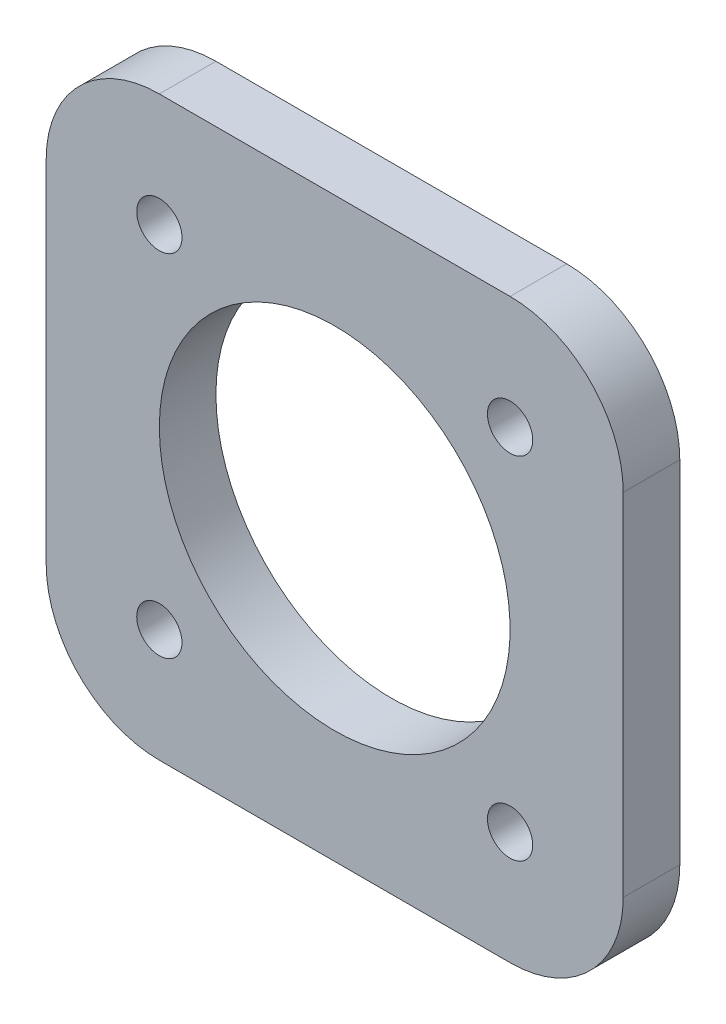
SolidWorks part; units mm, degrees
ref_plane "前视基准面" through (0, 0, 0) normal (0, 0, 1) x (1, 0, 0)
ref_plane "上视基准面" through (0, 0, 0) normal (0, 1, 0) x (1, 0, 0)
ref_plane "右视基准面" through (0, 0, 0) normal (1, 0, 0) x (0, 0, -1)
sketch "草图1" plane through (0, 0, 0) normal (0, 0, 1) x (1, 0, 0)
  line L0 (0, -38.5) -> (0, 38.5) construction
  line L1 (-15.5, -25.5) -> (15.5, -25.5)
  line L2 (-25.5, -15.5) -> (-25.5, 15.5)
  line L3 (-15.5, 25.5) -> (15.5, 25.5)
  line L4 (25.5, -15.5) -> (25.5, 15.5)
  line L5 (-25.5, -25.5) -> (25.5, 25.5) construction
  line L6 (-25.5, 25.5) -> (25.5, -25.5) construction
  line L7 (38.5, 0) -> (-38.5, 0) construction
  circle A0 centre (-15.5, 15.5) radius 2
  circle A1 centre (15.5, 15.5) radius 2
  circle A2 centre (15.5, -15.5) radius 2
  circle A3 centre (-15.5, -15.5) radius 2
  arc A4 (15.5, 25.5) -> (25.5, 15.5) centre (15.5, 15.5) cw
  arc A5 (15.5, -25.5) -> (25.5, -15.5) centre (15.5, -15.5) ccw
  arc A6 (-15.5, -25.5) -> (-25.5, -15.5) centre (-15.5, -15.5) cw
  arc A7 (-25.5, 15.5) -> (-15.5, 25.5) centre (-15.5, 15.5) cw
  point P0 (0, 0)
  dimension "D3" = 4
  dimension "D5" = 10
  dimension "D1" = 51
  dimension "D2" = 51
  dimension "D4" = 15.5
extrude "凸台-拉伸1" add sketch "草图1" along normal blind 5
sketch "草图2" plane through (0, 0, 0) normal (0, 0, 1) x (1, 0, 0)
  circle A0 centre (0, 0) radius 15.5
  dimension "D1" = 31
extrude "切除-拉伸1" cut sketch "草图2" along normal blind 30
